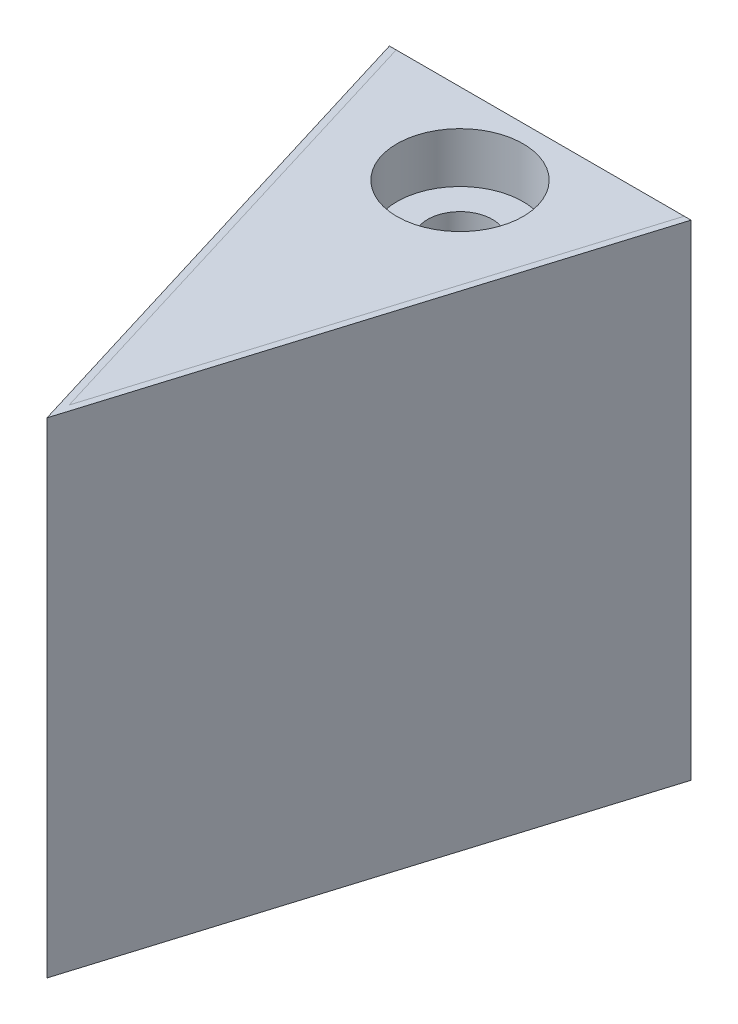
SolidWorks part; units mm, degrees
material "Plain Carbon Steel"
ref_plane "Front Plane" through (0, 0, 0) normal (0, 0, 1) x (1, 0, 0)
ref_plane "Top Plane" through (0, 0, 0) normal (0, 1, 0) x (1, 0, 0)
ref_plane "Right Plane" through (0, 0, 0) normal (1, 0, 0) x (0, 0, -1)
sketch "Sketch1" plane through (0, 0, 0) normal (0, 1, 0) x (1, 0, 0)
  line L0 (4.6424, -4.5654) -> (-4.6824, -4.5654)
  line L1 (-1.0137, -16.5654) -> (-4.6824, -4.5654)
  line L2 (-0.02, -19.8154) -> (-0.02, -4.5654) construction
  line L3 (0.9736, -16.5654) -> (4.6424, -4.5654)
  line L4 (-1.0137, -16.5654) -> (0.9736, -16.5654) construction
  line L8 (0.9736, -16.5654) -> (-0.02, -19.8154)
  line L9 (-0.02, -19.8154) -> (-1.0137, -16.5654)
  point P2 (-0.02, -16.5654)
  point P8 (-0.0154, 5.3291)
  dimension "D1" = 17
  dimension "D2" = 3.25
  dimension "D3" = 12
  dimension "D6" = 17
extrude "Boss-Extrude1" add sketch "Sketch1" along normal blind 12.5 and the other way blind 2.5
sketch "Sketch2" plane through (0, 0, 4.5654) normal (0, 0, -1) x (-1, 0, 0)
  line L0 (-4.6424, 12.5) -> (4.6824, -2.5) construction
  line L1 (4.6824, 12.5) -> (-4.6424, -2.5) construction
  line L3 (-2.8782, 5.95) -> (2.9183, 5.95)
  line L5 (-2.8782, 4.05) -> (2.9183, 4.05)
  arc A0 (-2.8782, 4.05) -> (2.9183, 4.05) centre (0.02, 5) ccw
  arc A1 (2.9183, 5.95) -> (-2.8782, 5.95) centre (0.02, 5) ccw
  dimension "D1" = 1.9
extrude "Cut-Extrude1" cut sketch "Sketch2" against normal blind 5
ref_plane "Plane2" through (0, 0, 10.0654) normal (0, 0, -1) x (-1, 0, 0)
ref_plane "Plane4" through (0, 0, 10.0654) normal (0, 0, -1) x (-1, 0, 0)
sketch "Sketch5" plane through (0, 5.74, 0) normal (0, 1, 0) x (1, 0, 0)
  line L3 (0.9955, -10.0654) -> (-0.9955, -10.0654) construction
  line L4 (4.6424, -4.5654) -> (-4.6824, -4.5654) construction
  circle A0 centre (0, -7.0654) radius 1
  dimension "D1" = 3
  dimension "D2" = 2.5
extrude "Cut-Extrude2" cut sketch "Sketch5" against normal through all and the other way through all
sketch "Sketch6" plane through (0, 12.5, 0) normal (0, 1, 0) x (1, 0, 0)
  circle A0 centre (0, -7.0654) radius 1.95
extrude "Cut-Extrude3" cut sketch "Sketch6" against normal blind 1.55 contours A0
sketch "Sketch7" plane through (0, 12.5, 0) normal (0, 1, 0) x (1, 0, 0)
  line L0 (-4.6824, -4.5654) -> (-0.02, -19.8154)
  line L2 (-0.02, -19.8154) -> (4.6424, -4.5654)
  line L4 (-4.4733, -4.5654) -> (-0.02, -19.1313)
  line L6 (-0.02, -19.1313) -> (4.4332, -4.5654)
  line L7 (-4.6824, -4.5654) -> (-4.4733, -4.5654)
  line L8 (4.6424, -4.5654) -> (4.4332, -4.5654)
  line L9 (4.6424, -4.5654) -> (-4.6824, -4.5654) construction
  line L10 (-0.02, -19.1313) -> (4.4511, -4.5069) construction
  line L11 (-4.4912, -4.5069) -> (-0.02, -19.1313) construction
  dimension "D1" = 0.2
split "Split2" trim tools "Sketch7" bodies to split 114 resulting bodies 117 118
